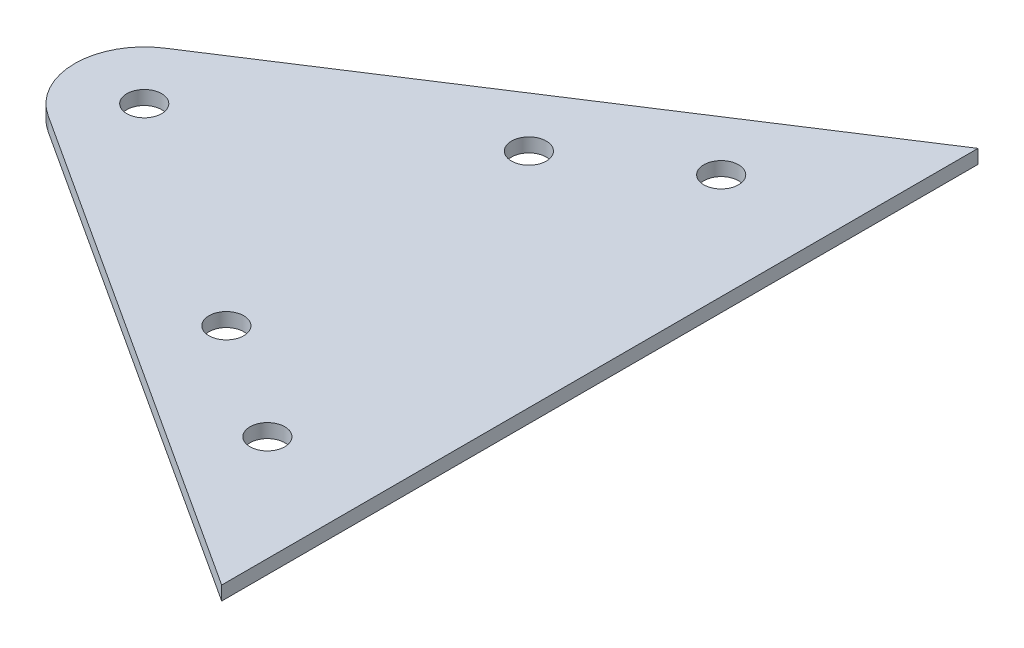
SolidWorks part; units mm, degrees
ref_plane "Front Plane" through (0, 0, 0) normal (0, 0, 1) x (1, 0, 0)
ref_plane "Top Plane" through (0, 0, 0) normal (0, 1, 0) x (1, 0, 0)
ref_plane "Right Plane" through (0, 0, 0) normal (1, 0, 0) x (0, 0, -1)
sketch "Sketch2" plane through (0, 0, 0) normal (0, 1, 0) x (1, 0, 0)
  line L0 (14.3932, 58.6406) -> (-56.575, 12.6414)
  line L1 (-56.575, -4.1415) -> (14.3932, -50.1408)
  line L2 (14.3932, -50.1408) -> (14.3932, 58.6406)
  circle A0 centre (-51.1359, 4.2499) radius 2.5
  circle A1 centre (-17.5701, 26.0062) radius 2.5
  circle A2 centre (-0.7871, 36.8844) radius 2.5
  circle A3 centre (-17.5701, -17.5063) radius 2.5
  circle A4 centre (-0.7871, -28.3845) radius 2.5
  arc A5 (-56.575, 12.6414) -> (-56.575, -4.1415) centre (-51.1359, 4.2499) ccw
  point P15 (-69.5214, 4.2499)
  dimension "D4" = 5
  dimension "D5" = 5
  dimension "D6" = 5
  dimension "D7" = 5
  dimension "D8" = 5
  dimension "D19" = 10
  dimension "D1" = 65.9
  dimension "D2" = 100
  dimension "D3" = 100
  dimension "D9" = 10
  dimension "D10" = 10
  dimension "D11" = 10
  dimension "D12" = 10
  dimension "D13" = 10
  dimension "D14" = 10
  dimension "D15" = 40
  dimension "D16" = 20
  dimension "D17" = 40
  dimension "D18" = 20
extrude "Boss-Extrude2" add sketch "Sketch2" along normal blind 2
